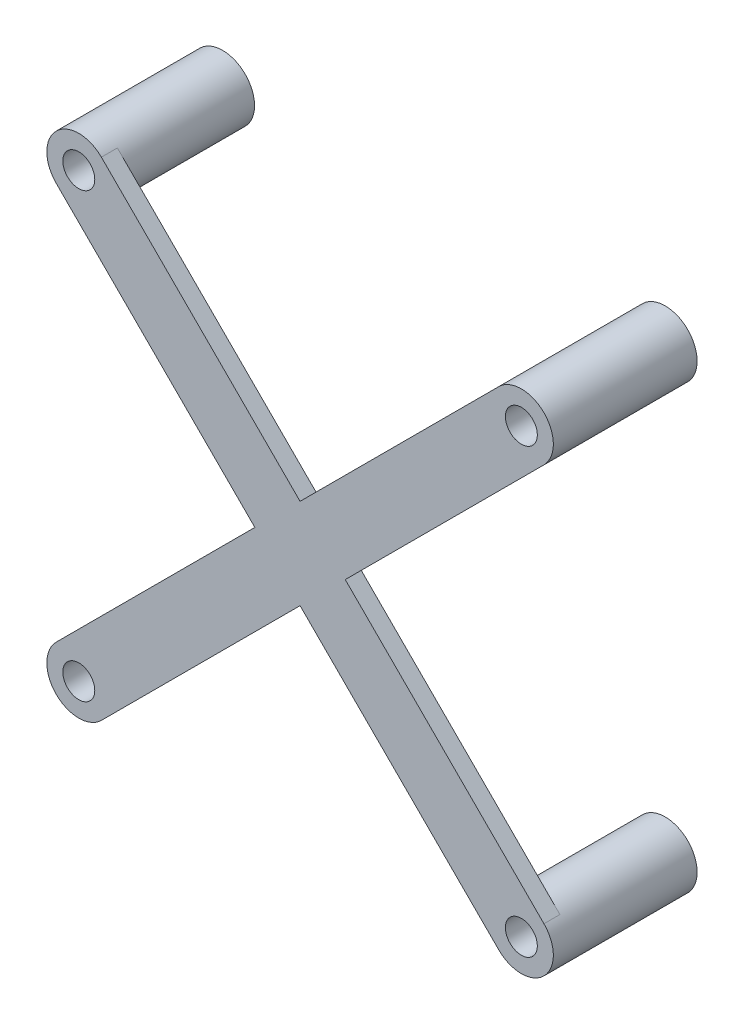
SolidWorks part; units mm, degrees
ref_plane "Front Plane" through (0, 0, 0) normal (1, 0, 0) x (0, 1, 0)
ref_plane "Top Plane" through (0, 0, 0) normal (0, 0, 1) x (0, 1, 0)
ref_plane "Right Plane" through (0, 0, 0) normal (0, 1, 0) x (-1, 0, 0)
sketch "Camera Holes" plane through (0, 0, 0) normal (0, 0, 1) x (0, 1, 0)
  line L0 (13.85, -12.85) -> (13.85, 12.85)
  line L5 (12.85, 13.85) -> (-12.85, 13.85)
  line L6 (-13.85, 12.85) -> (-13.85, -12.85)
  line L7 (-12.85, -13.85) -> (12.85, -13.85)
  line L8 (-13.85, 0) -> (13.85, 0) construction
  line L9 (0, 13.85) -> (0, -13.85) construction
  circle A0 centre (13.85, 13.85) radius 1
  circle A1 centre (13.85, -13.85) radius 1
  circle A2 centre (-13.85, 13.85) radius 1
  circle A3 centre (-13.85, -13.85) radius 1
  point P21 (0, 0)
  dimension "D2" = 25.7
  dimension "D1" = 2
sketch "Dist b/w camera bracket holes" plane through (0, 0, 0) normal (0, 0, 1) x (0, 1, 0)
  line L0 (0, 13.85) -> (0, -13.85) construction
  line L1 (-13.85, 0) -> (13.85, 0) construction
  line L2 (-13.85, 0) -> (13.85, 0) construction
  line L3 (0, 13.85) -> (0, -13.85) construction
  circle A0 centre (-10.67, 11.135) radius 1
  circle A1 centre (-10.67, -11.135) radius 1
  circle A2 centre (10.67, -11.135) radius 1
  circle A3 centre (10.67, 11.135) radius 1
  dimension "D1" = 2
  dimension "D2" = 21.34
  dimension "D3" = 22.27
sketch "Sketch3" plane through (0, 0, 0) normal (0, 0, 1) x (0, 1, 0)
  circle A10 centre (-13.85, 13.85) radius 2
  circle A12 centre (13.85, 13.85) radius 2
  circle A14 centre (13.85, -13.85) radius 2
  circle A16 centre (-13.85, -13.85) radius 2
  point P21 (0, 0)
  dimension "D1" = 4
  dimension "D3" = 4
extrude "Boss-Extrude1" add sketch "Sketch3" along normal blind 8
sketch "Sketch4" plane through (0, 0, 8) normal (0, 0, 1) x (1, 0, 0)
  line L20 (-13.85, -13.85) -> (13.85, 13.85) construction
  line L21 (-15.2642, -12.4358) -> (-2.8284, 0)
  line L22 (-12.4358, -15.2642) -> (0, -2.8284)
  line L23 (-13.85, 13.85) -> (13.85, -13.85) construction
  line L24 (-12.4358, 15.2642) -> (0, 2.8284)
  line L25 (-15.2642, 12.4358) -> (-2.8284, 0)
  line L26 (0, 2.8284) -> (12.4358, 15.2642)
  line L27 (2.8284, 0) -> (15.2642, 12.4358)
  line L28 (0, -2.8284) -> (12.4358, -15.2642)
  line L29 (2.8284, 0) -> (15.2642, -12.4358)
  arc A12 (-15.2642, -12.4358) -> (-12.4358, -15.2642) centre (-13.85, -13.85) ccw
  arc A13 (15.2642, 12.4358) -> (12.4358, 15.2642) centre (13.85, 13.85) ccw
  arc A14 (-12.4358, 15.2642) -> (-15.2642, 12.4358) centre (-13.85, 13.85) ccw
  arc A15 (12.4358, -15.2642) -> (15.2642, -12.4358) centre (13.85, -13.85) ccw
  circle A16 centre (13.85, -13.85) radius 2 construction
  point P4 (0, 0)
  point P11 (0, 0)
extrude "Boss-Extrude2" add sketch "Sketch4" along normal blind 1
sketch "Sketch5" plane through (0, 0, 0) normal (0, 0, 1) x (0, 1, 0)
  circle A0 centre (-13.85, 13.85) radius 1
  circle A1 centre (13.85, 13.85) radius 1
  circle A2 centre (13.85, -13.85) radius 1
  circle A3 centre (-13.85, -13.85) radius 1
  point P12 (0, 0)
  dimension "D1" = 2
  dimension "D2" = 4
extrude "Cut-Extrude1" cut sketch "Sketch5" along normal through all both and the other way through all
